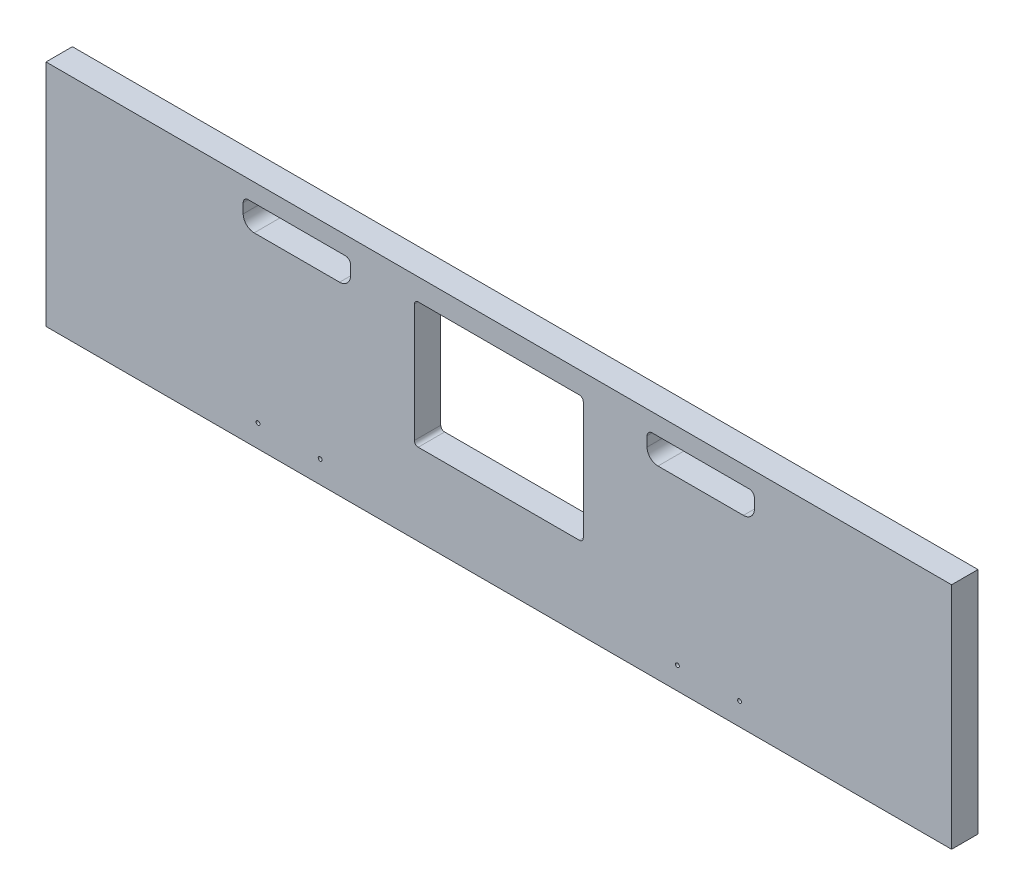
SolidWorks part; units mm, degrees
material "Pine"
ref_plane "Front Plane" through (0, 0, 0) normal (0, 0, 1) x (1, 0, 0)
ref_plane "Top Plane" through (0, 0, 0) normal (0, 1, 0) x (1, 0, 0)
ref_plane "Right Plane" through (0, 0, 0) normal (1, 0, 0) x (0, 0, -1)
sketch "Sketch1" plane through (0, 0, 0) normal (0, 0, 1) x (1, 0, 0)
  line L0 (-163.9887, -5335.905) -> (-163.9887, -5432.425)
  line L1 (-102.87, -5350.891) -> (-33.02, -5350.891)
  line L2 (-111.8235, -5341.9375) -> (-111.8235, -5334)
  line L3 (-24.0665, -5341.9375) -> (-24.0665, -5334)
  line L4 (-298.9262, -5332.73) -> (-167.1637, -5332.73)
  line L5 (-167.1637, -5435.6) -> (-298.9262, -5435.6)
  line L6 (-302.1012, -5432.425) -> (-302.1012, -5335.905)
  line L7 (-107.6325, -5329.809) -> (-28.2575, -5329.809)
  line L8 (174.9425, -5308.6) -> (174.9425, -5581.65)
  line L9 (449.2625, -5413.1661) -> (449.2625, -5421.9659)
  line L10 (595.3125, -5421.9659) -> (595.3125, -5413.1661)
  line L11 (839.47, -5509.5521) -> (839.47, -5307.6729)
  line L12 (839.47, -5307.6729) -> (863.6, -5307.6729)
  line L13 (839.47, -5509.5521) -> (863.6, -5509.5521)
  line L14 (863.6, -5509.5521) -> (863.6, -5307.6729)
  line L15 (-354.2665, -5341.9375) -> (-354.2665, -5334)
  line L16 (-100.8856, -5889.625) -> (-50.0856, -5889.625)
  line L17 (-104.0606, -5969) -> (-104.0606, -5892.8)
  line L18 (-46.9106, -5892.8) -> (-46.9106, -5969)
  line L19 (-50.0856, -5972.175) -> (-100.8856, -5972.175)
  line L20 (-100.8856, -5848.35) -> (-50.0856, -5848.35)
  line L21 (857.25, -5502.275) -> (157.1625, -5575.3)
  line L22 (857.25, -5314.95) -> (857.25, -5502.275)
  line L23 (157.1625, -5314.95) -> (157.1625, -5575.3)
  line L24 (857.25, -5314.95) -> (157.1625, -5314.95)
  line L25 (150.8125, -5308.6) -> (174.9425, -5308.6)
  line L26 (174.9425, -5581.65) -> (150.8125, -5581.65)
  line L27 (137.16, -5314.95) -> (137.16, -5502.275)
  line L28 (150.8125, -5581.65) -> (150.8125, -5308.6)
  line L29 (590.8224, -5408.676) -> (453.7526, -5408.676)
  line L30 (453.7526, -5426.456) -> (590.8224, -5426.456)
  line L31 (137.16, -6013.45) -> (137.16, -5867.4)
  line L32 (150.8125, -5746.75) -> (150.8125, -6019.8)
  line L33 (143.51, -5639.9938) -> (143.51, -5654.294)
  line L34 (590.8224, -5919.724) -> (453.7526, -5919.724)
  line L35 (453.7526, -5901.944) -> (590.8224, -5901.944)
  line L36 (449.2625, -5915.2339) -> (449.2625, -5906.4341)
  line L37 (174.9425, -6019.8) -> (174.9425, -5746.75)
  line L38 (595.3125, -5906.4341) -> (595.3125, -5915.2339)
  line L39 (839.47, -5818.8479) -> (839.47, -6020.7271)
  line L40 (839.47, -5818.8479) -> (863.6, -5818.8479)
  line L41 (863.6, -5818.8479) -> (863.6, -6020.7271)
  line L42 (839.47, -6020.7271) -> (863.6, -6020.7271)
  line L43 (-155.8782, -5867.4) -> (-603.25, -5867.4)
  line L44 (-433.07, -5350.891) -> (-363.22, -5350.891)
  line L45 (-437.8325, -5329.809) -> (-358.4575, -5329.809)
  line L46 (889, -6045.2) -> (-635, -6045.2)
  line L47 (-635, -5283.2) -> (889, -5283.2)
  line L48 (-635, -6045.2) -> (-635, -5283.2)
  line L49 (889, -5283.2) -> (889, -6045.2)
  line L50 (137.16, -5502.275) -> (-603.25, -5502.275)
  line L51 (-603.25, -5314.95) -> (137.16, -5314.95)
  line L52 (143.51, -5654.294) -> (-609.6, -5654.294)
  line L53 (-609.6, -5639.9938) -> (143.51, -5639.9938)
  line L54 (137.16, -5536.0062) -> (-603.25, -5536.0062)
  line L55 (-603.25, -5794.375) -> (137.16, -5794.375)
  line L56 (-603.25, -6013.45) -> (137.16, -6013.45)
  line L57 (-603.25, -5536.0062) -> (-603.25, -5794.375)
  line L58 (137.16, -5794.375) -> (137.16, -5536.0062)
  line L59 (-609.6, -5654.294) -> (-609.6, -5639.9938)
  line L60 (-603.25, -5867.4) -> (-603.25, -6013.45)
  line L61 (-603.25, -5314.95) -> (-603.25, -5502.275)
  line L62 (-442.0235, -5341.9375) -> (-442.0235, -5334)
  line L63 (857.25, -5826.125) -> (157.1625, -5753.1)
  line L64 (857.25, -6013.45) -> (857.25, -5826.125)
  line L65 (157.1625, -6013.45) -> (157.1625, -5753.1)
  line L66 (857.25, -6013.45) -> (157.1625, -6013.45)
  line L67 (174.9425, -5746.75) -> (150.8125, -5746.75)
  line L68 (150.8125, -6019.8) -> (174.9425, -6019.8)
  line L69 (137.16, -5867.4) -> (4.907, -5867.4)
  circle A0 centre (-36.195, -5484.0124) radius 1.5875
  arc A1 (-298.9262, -5332.73) -> (-302.1012, -5335.905) centre (-298.9262, -5335.905) ccw
  arc A2 (-302.1012, -5432.425) -> (-298.9262, -5435.6) centre (-298.9262, -5432.425) ccw
  arc A3 (-163.9887, -5335.905) -> (-167.1637, -5332.73) centre (-167.1637, -5335.905) ccw
  arc A4 (-167.1637, -5435.6) -> (-163.9887, -5432.425) centre (-167.1637, -5432.425) ccw
  arc A5 (-111.8235, -5341.9375) -> (-102.87, -5350.891) centre (-102.87, -5341.9375) ccw
  arc A6 (-107.6325, -5329.809) -> (-111.8235, -5334) centre (-107.6325, -5334) ccw
  circle A7 centre (166.0525, -5444.6613) radius 1.5875
  circle A8 centre (166.0525, -5358.1871) radius 1.5875
  circle A9 centre (471.4875, -5417.566) radius 1.5875
  arc A10 (453.7526, -5408.676) -> (449.2625, -5413.1661) centre (451.5076, -5410.9211) ccw
  arc A11 (449.2625, -5421.9659) -> (453.7526, -5426.456) centre (451.5076, -5424.2109) ccw
  circle A12 centre (522.2875, -5417.566) radius 1.5875
  circle A13 centre (573.0875, -5417.566) radius 1.5875
  arc A14 (590.8224, -5426.456) -> (595.3125, -5421.9659) centre (593.0674, -5424.2109) ccw
  arc A15 (595.3125, -5413.1661) -> (590.8224, -5408.676) centre (593.0674, -5410.9211) ccw
  circle A16 centre (848.36, -5471.8269) radius 1.5875
  circle A17 centre (848.36, -5409.0762) radius 1.5875
  circle A18 centre (848.36, -5346.3254) radius 1.5875
  arc A19 (-363.22, -5350.891) -> (-354.2665, -5341.9375) centre (-363.22, -5341.9375) ccw
  arc A20 (-354.2665, -5334) -> (-358.4575, -5329.809) centre (-358.4575, -5334) ccw
  arc A21 (-24.0665, -5334) -> (-28.2575, -5329.809) centre (-28.2575, -5334) ccw
  arc A22 (-33.02, -5350.891) -> (-24.0665, -5341.9375) centre (-33.02, -5341.9375) ccw
  circle A23 centre (-86.995, -5484.0124) radius 1.5875
  circle A24 centre (-333.4544, -5894.07) radius 2.54
  circle A25 centre (-333.4544, -5994.4) radius 2.54
  arc A26 (-104.0606, -5969) -> (-100.8856, -5972.175) centre (-100.8856, -5969) ccw
  arc A27 (-50.0856, -5972.175) -> (-46.9106, -5969) centre (-50.0856, -5969) ccw
  arc A28 (-100.8856, -5848.35) -> (-128.3819, -5857.875) centre (-100.8856, -5892.8) ccw
  arc A29 (-155.8782, -5867.4) -> (-128.3819, -5857.875) centre (-155.8782, -5822.95) ccw
  arc A30 (-22.5893, -5857.875) -> (-50.0856, -5848.35) centre (-50.0856, -5892.8) ccw
  circle A31 centre (-132.6356, -5894.07) radius 2.54
  circle A32 centre (-132.6356, -5994.4) radius 2.54
  arc A33 (-46.9106, -5892.8) -> (-50.0856, -5889.625) centre (-50.0856, -5892.8) ccw
  arc A34 (-100.8856, -5889.625) -> (-104.0606, -5892.8) centre (-100.8856, -5892.8) ccw
  arc A35 (-22.5893, -5857.875) -> (4.907, -5867.4) centre (4.907, -5822.95) ccw
  circle A36 centre (166.0525, -5531.1356) radius 1.5875
  arc A37 (449.2625, -5915.2339) -> (453.7526, -5919.724) centre (451.5076, -5917.4789) ccw
  arc A38 (453.7526, -5901.944) -> (449.2625, -5906.4341) centre (451.5076, -5904.1891) ccw
  circle A39 centre (166.0525, -5797.2644) radius 1.5875
  circle A40 centre (166.0525, -5883.7387) radius 1.5875
  circle A41 centre (166.0525, -5970.2129) radius 1.5875
  circle A42 centre (471.4875, -5910.834) radius 1.5875
  circle A43 centre (522.2875, -5910.834) radius 1.5875
  circle A44 centre (573.0875, -5910.834) radius 1.5875
  arc A45 (595.3125, -5906.4341) -> (590.8224, -5901.944) centre (593.0674, -5904.1891) ccw
  arc A46 (590.8224, -5919.724) -> (595.3125, -5915.2339) centre (593.0674, -5917.4789) ccw
  circle A47 centre (848.36, -5919.3238) radius 1.5875
  circle A48 centre (848.36, -5982.0746) radius 1.5875
  circle A49 centre (848.36, -5856.5731) radius 1.5875
  arc A50 (-437.8325, -5329.809) -> (-442.0235, -5334) centre (-437.8325, -5334) ccw
  circle A51 centre (-429.895, -5484.0124) radius 1.5875
  arc A52 (-442.0235, -5341.9375) -> (-433.07, -5350.891) centre (-433.07, -5341.9375) ccw
  circle A53 centre (-379.095, -5484.0124) radius 1.5875
sketch "Sketch2" plane through (0, 0, 0) normal (0, 0, 1) x (1, 0, 0)
  line L0 (137.16, -5502.275) -> (137.16, -5314.95)
  line L1 (137.16, -5314.95) -> (-603.25, -5314.95)
  line L2 (-603.25, -5314.95) -> (-603.25, -5502.275)
  line L3 (-603.25, -5502.275) -> (137.16, -5502.275)
extrude "Extrude1" add sketch "Sketch2" against normal blind 21.59
sketch "Sketch3" plane through (0, 0, 0) normal (0, 0, 1) x (1, 0, 0)
  line L0 (-302.1012, -5335.905) -> (-302.1012, -5432.425)
  line L1 (-298.9262, -5435.6) -> (-167.1637, -5435.6)
  line L2 (-163.9887, -5432.425) -> (-163.9887, -5335.905)
  line L3 (-167.1637, -5332.73) -> (-298.9262, -5332.73)
  line L4 (-354.2665, -5334) -> (-354.2665, -5341.9375)
  line L5 (-363.22, -5350.891) -> (-433.07, -5350.891)
  line L6 (-442.0235, -5341.9375) -> (-442.0235, -5334)
  line L7 (-437.8325, -5329.809) -> (-358.4575, -5329.809)
  line L8 (-102.87, -5350.891) -> (-33.02, -5350.891)
  line L9 (-24.0665, -5341.9375) -> (-24.0665, -5334)
  line L10 (-28.2575, -5329.809) -> (-107.6325, -5329.809)
  line L11 (-111.8235, -5334) -> (-111.8235, -5341.9375)
  arc A0 (-302.1012, -5432.425) -> (-298.9262, -5435.6) centre (-298.9262, -5432.425) ccw
  arc A1 (-167.1637, -5435.6) -> (-163.9887, -5432.425) centre (-167.1637, -5432.425) ccw
  arc A2 (-163.9887, -5335.905) -> (-167.1637, -5332.73) centre (-167.1638, -5335.905) ccw
  arc A3 (-298.9262, -5332.73) -> (-302.1012, -5335.905) centre (-298.9262, -5335.905) ccw
  arc A4 (-354.2665, -5341.9375) -> (-363.22, -5350.891) centre (-363.22, -5341.9375) cw
  arc A5 (-433.07, -5350.891) -> (-442.0235, -5341.9375) centre (-433.07, -5341.9375) cw
  arc A6 (-442.0235, -5334) -> (-437.8325, -5329.809) centre (-437.8325, -5334) cw
  arc A7 (-358.4575, -5329.809) -> (-354.2665, -5334) centre (-358.4575, -5334) cw
  arc A8 (-33.02, -5350.891) -> (-24.0665, -5341.9375) centre (-33.02, -5341.9375) ccw
  arc A9 (-24.0665, -5334) -> (-28.2575, -5329.809) centre (-28.2575, -5334) ccw
  arc A10 (-107.6325, -5329.809) -> (-111.8235, -5334) centre (-107.6325, -5334) ccw
  arc A11 (-111.8235, -5341.9375) -> (-102.87, -5350.891) centre (-102.87, -5341.9375) ccw
  circle A12 centre (-429.895, -5484.0124) radius 1.5875
  circle A13 centre (-379.095, -5484.0124) radius 1.5875
  circle A14 centre (-86.995, -5484.0124) radius 1.5875
  circle A15 centre (-36.195, -5484.0124) radius 1.5875
extrude "Cut-Extrude1" cut sketch "Sketch3" against normal up to surface (21.59 mm away) up to face at (-233.045, -5408.6125, -21.59)
